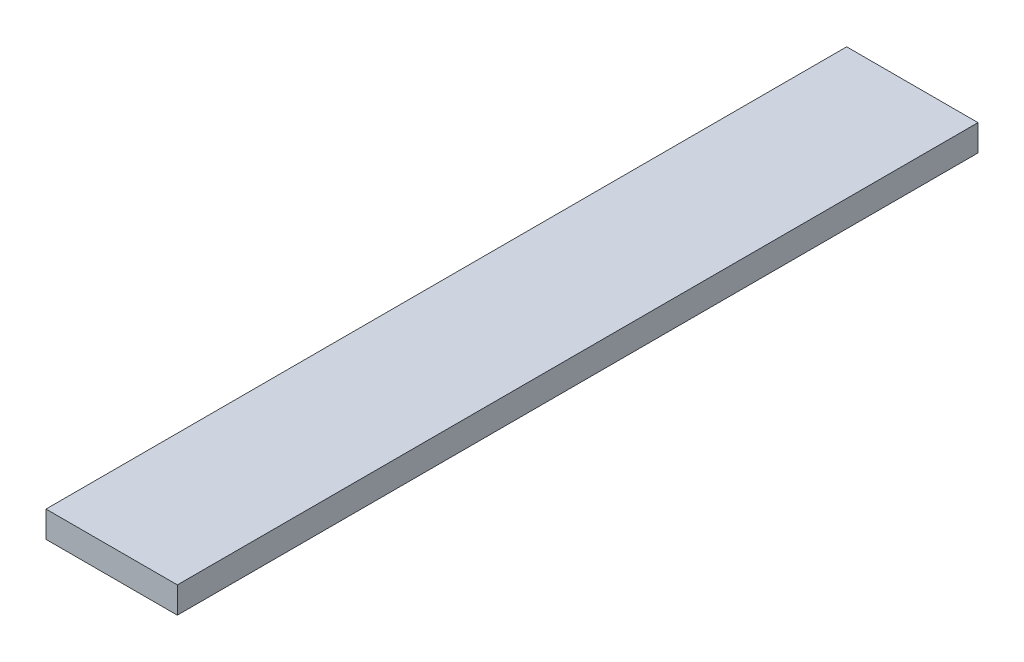
SolidWorks part; units mm, degrees
ref_plane "Front Plane" through (0, 0, 0) normal (0, 0, 1) x (1, 0, 0)
ref_plane "Top Plane" through (0, 0, 0) normal (0, 1, 0) x (1, 0, 0)
ref_plane "Right Plane" through (0, 0, 0) normal (1, 0, 0) x (0, 0, -1)
sketch "Sketch1" plane through (0, 0, 0) normal (0, 0, 1) x (1, 0, 0)
  line L0 (-25, 0) -> (25, 0) construction
  line L1 (0, -5) -> (0, 5) construction
  line L5 (-25, 5) -> (25, 5) construction
  line L7 (-25, 5) -> (-25, -5) construction
  line L8 (25, -5) -> (25, 5) construction
  line L13 (-25, -5) -> (25, -5) construction
  point P0 (0, 0)
  point P4 (0, 0)
  point P9 (0, 0)
  point P22 (0, 5)
  dimension "Thickness" = 10
  dimension "D1" = 50
sketch "Sketch2" plane through (0, 0, 0) normal (0, 1, 0) x (0, 0, -1)
  line L0 (152.4, 0) -> (-152.4, 0) construction
  line L2 (-152.4, 25) -> (152.4, 25) construction
  line L3 (-152.4, 25) -> (-152.4, -25) construction
  line L4 (-152.4, -25) -> (152.4, -25) construction
  line L5 (152.4, 25) -> (152.4, -25) construction
  line L6 (-152.4, 25) -> (152.4, -25) construction
  line L7 (-152.4, -25) -> (152.4, 25) construction
  point P4 (0, 0)
  point P7 (0, 0)
  point P12 (-94.9, 25)
  point P13 (94.9, 25)
  dimension "Length" = 304.8
  dimension "Width" = 50
  dimension "D1" = 57.5
  dimension "D2" = 57.5
sketch "Sketch3" plane through (0, 0, 0) normal (0, 0, 1) x (1, 0, 0)
  line L3 (-25, 5) -> (25, 5)
  line L17 (25, 5) -> (25, -5)
  line L18 (25, -5) -> (-25, -5)
  line L19 (-25, -5) -> (-25, 5)
extrude "Boss-Extrude1" add sketch "Sketch3" along normal mid plane 304.8
equation "\"D1@Boss-Extrude1\" = \"Length@Sketch2\""
equation "\"D1@Sketch1\"=\"Width@Sketch2\""
equation "\"D1@Sketch2\"=\"Width@Sketch2\"*1.15"
equation "\"D2@Sketch2\"=\"D1@Sketch2\""
